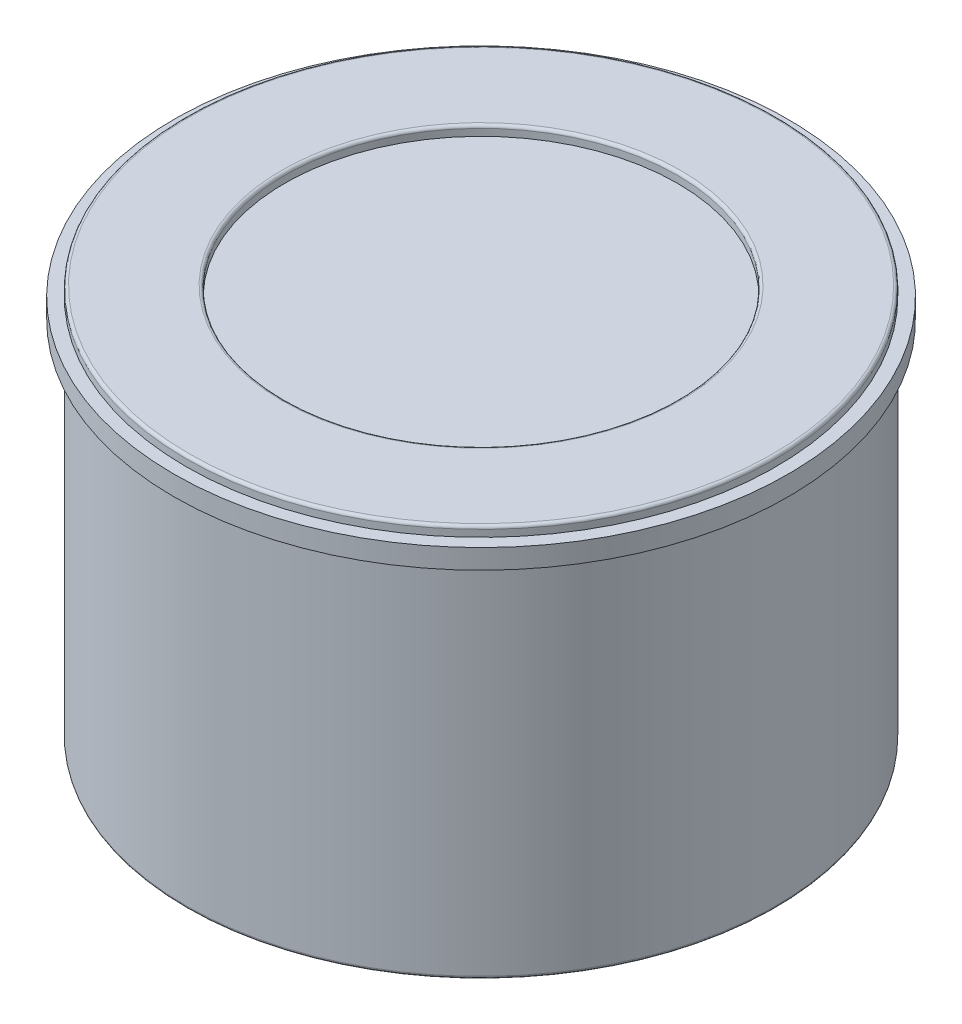
SolidWorks part; units mm, degrees
material "Sade Karbon Çeliği"
ref_plane "Ön Düzlem" through (0, 0, 0) normal (0, 0, 1) x (1, 0, 0)
ref_plane "Üst Düzlem" through (0, 0, 0) normal (0, 1, 0) x (1, 0, 0)
ref_plane "Sağ Düzlem" through (0, 0, 0) normal (1, 0, 0) x (0, 0, -1)
sketch "Çizim1" plane through (0, 0, 0) normal (0, 1, 0) x (1, 0, 0)
  circle A0 centre (0, 0) radius 15
extrude "Yükseklik-Ekstrüzyon2" add sketch "Çizim1" along normal blind 20
sketch "Çizim2" plane through (0, 20, 0) normal (0, 1, 0) x (1, 0, 0)
  circle A3 centre (0, 0) radius 10
  circle A4 centre (0, 0) radius 10
  dimension "D1" = 5
extrude "Kes-Ekstrüzyon1" cut sketch "Çizim2" against normal blind 1
sketch "Çizim3" plane through (0, 0, 0) normal (0, -1, 0) x (1, 0, 0)
  circle A2 centre (0, 0) radius 10
  circle A3 centre (0, 0) radius 10
  dimension "D1" = 5
extrude "Kes-Ekstrüzyon2" cut sketch "Çizim3" against normal blind 3
sketch "Çizim4" plane through (0, 3, 0) normal (0, -1, 0) x (1, 0, 0)
  line L1 (-2, 2) -> (2, 2)
  line L2 (-2, 2) -> (-2, -2)
  line L3 (-2, -2) -> (2, -2)
  line L4 (2, 2) -> (2, -2)
  line L5 (-2, 2) -> (2, -2) construction
  line L6 (-2, -2) -> (2, 2) construction
  point P0 (0, 0)
  dimension "D1" = 4
  dimension "D2" = 4
extrude "Yükseklik-Ekstrüzyon3" add sketch "Çizim4" along normal blind 7
sketch "Çizim5" plane through (2, 0, 0) normal (1, 0, 0) x (0, 0, -1)
  line L0 (-2, -4) -> (2, 0)
  line L1 (16.5, 0) -> (-16.5, 0) construction
  circle A0 centre (0, -2) radius 1.5
extrude "Kes-Ekstrüzyon3" cut sketch "Çizim5" against normal blind 7 contours L0 A0 | L0 A0
fillet "Radyus1" radius 0.15 6 edges at (0, 20, 10) (0, 20, 15) (0, 0, 15) (0, 0, -10) (0, -4, -2) (0, -4, 2)
sketch "Çizim6" plane through (0, 20, 0) normal (0, 1, 0) x (1, 0, 0)
  circle A0 centre (0, 0) radius 15.6367
extrude "Yükseklik-Ekstrüzyon4" add sketch "Çizim6" against normal blind 1 from offset 0.5
